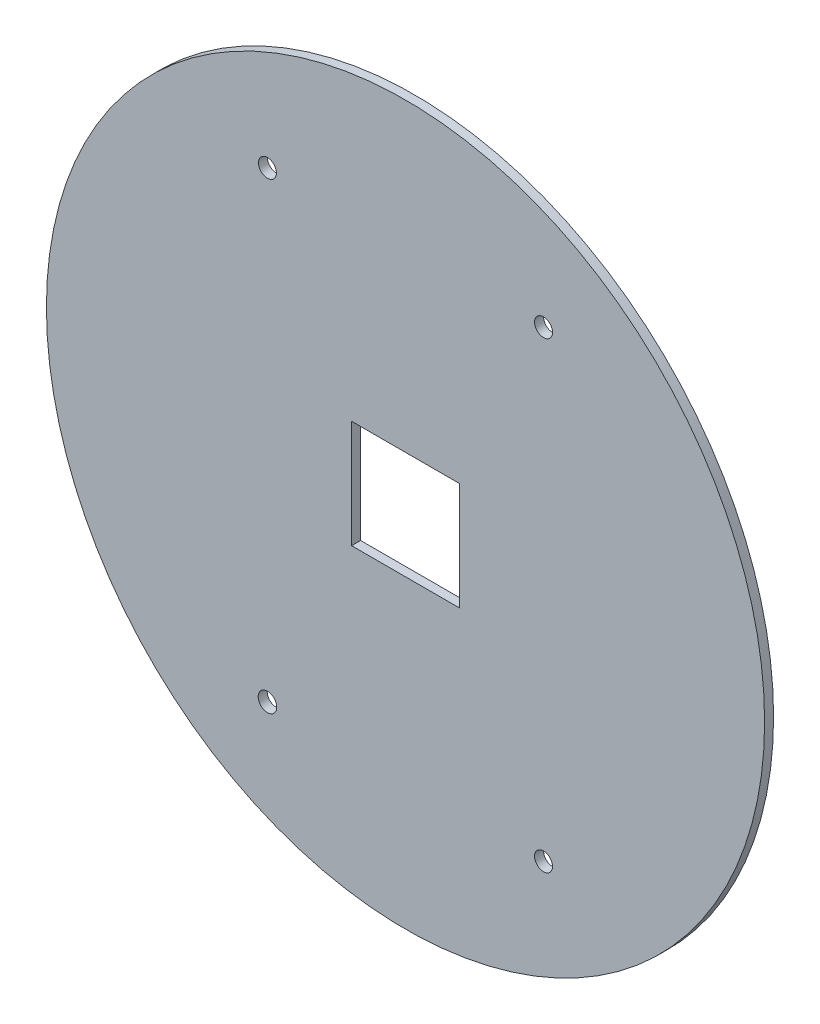
SolidWorks part; units mm, degrees
ref_plane "Front Plane" through (0, 0, 0) normal (0, 0, 1) x (1, 0, 0)
ref_plane "Top Plane" through (0, 0, 0) normal (0, 1, 0) x (1, 0, 0)
ref_plane "Right Plane" through (0, 0, 0) normal (1, 0, 0) x (0, 0, -1)
sketch "Sketch1" plane through (0, 0, 0) normal (0, 0, 1) x (1, 0, 0)
  line L1 (-30, 30) -> (30, 30)
  line L2 (-30, 30) -> (-30, -30)
  line L3 (-30, -30) -> (30, -30)
  line L4 (30, 30) -> (30, -30)
  line L5 (-30, 30) -> (30, -30) construction
  line L6 (-30, -30) -> (30, 30) construction
  circle A0 centre (0, 0) radius 200
  circle A1 centre (-76.8972, 128.7898) radius 5
  circle A2 centre (-76.8802, -128.8) radius 5.1676
  circle A3 centre (76.8802, 128.8) radius 5
  circle A4 centre (76.8802, -128.8) radius 5
  point P7 (30, 0)
  dimension "D1" = 400
  dimension "D4" = 10
  dimension "D5" = 128.7898
  dimension "D9" = 10
  dimension "D10" = 10
  dimension "D2" = 30
  dimension "D3" = 60
  dimension "D6" = 150
  dimension "D7" = 150
  dimension "D8" = 128.8
  dimension "D11" = 150
  dimension "D12" = 150
  dimension "D13" = 128.8
  dimension "D14" = 128.8
extrude "Boss-Extrude2" add sketch "Sketch1" along normal blind 5
